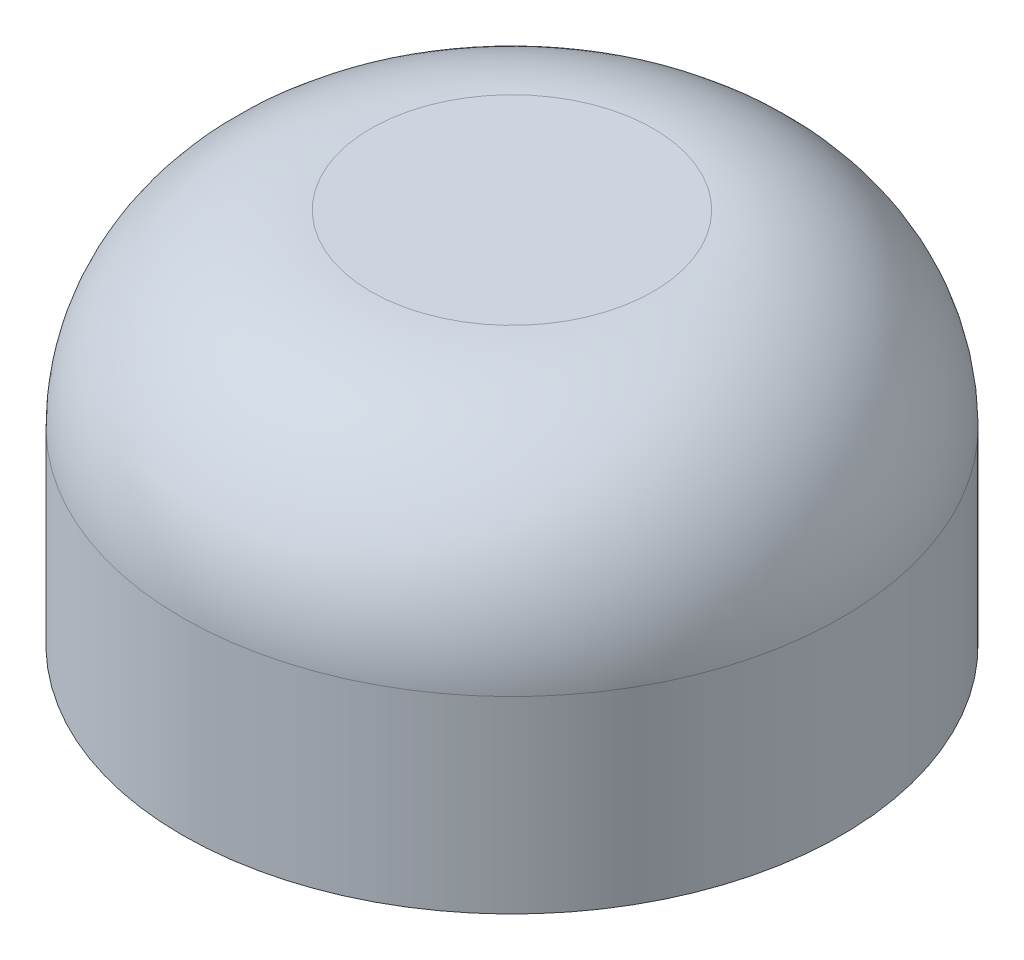
SolidWorks part; units mm, degrees
ref_plane "Front Plane" through (0, 0, 0) normal (0, 0, 1) x (1, 0, 0)
ref_plane "Top Plane" through (0, 0, 0) normal (0, 1, 0) x (1, 0, 0)
ref_plane "Right Plane" through (0, 0, 0) normal (1, 0, 0) x (0, 0, -1)
sketch "Sketch1" plane through (0, 0, 0) normal (0, 1, 0) x (1, 0, 0)
  circle A0 centre (0, 0) radius 1.75
  dimension "D1" = 3.5
extrude "Boss-Extrude1" add sketch "Sketch1" along normal blind 2
fillet "Fillet1" radius 1 1 edges at (0, 2, 1.75)
ref_point "Point1"
